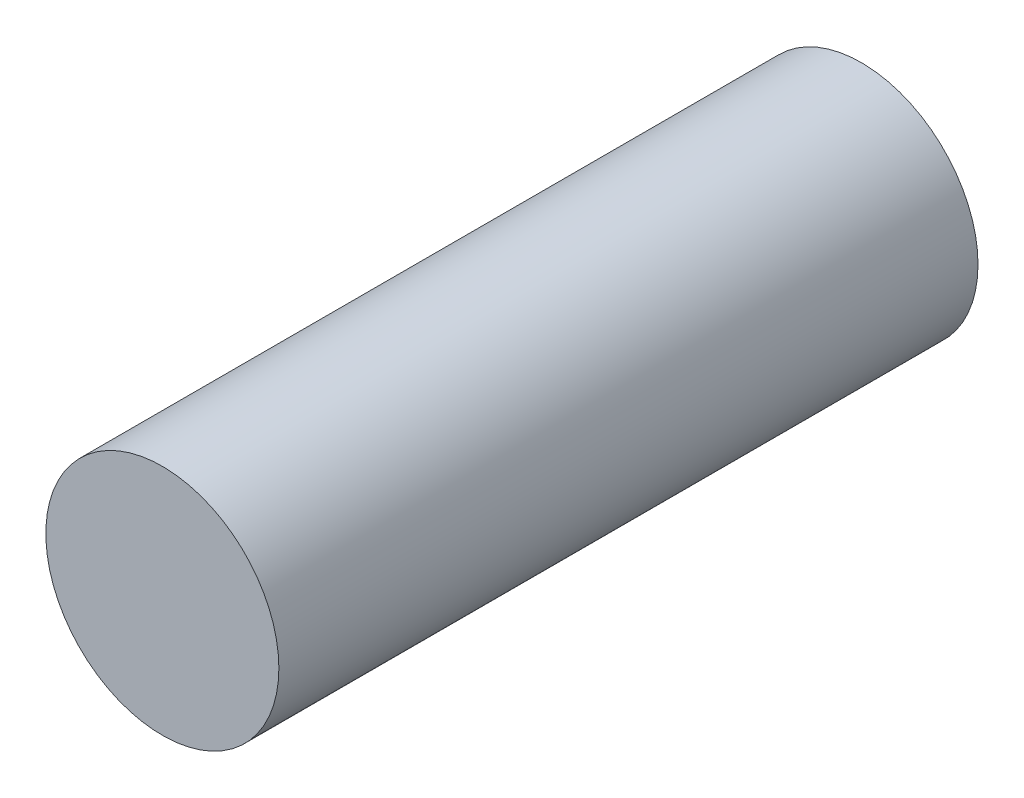
SolidWorks part; units mm, degrees
ref_plane "Alzado" through (0, 0, 0) normal (0, 0, 1) x (1, 0, 0)
ref_plane "Planta" through (0, 0, 0) normal (0, 1, 0) x (1, 0, 0)
ref_plane "Vista lateral" through (0, 0, 0) normal (1, 0, 0) x (0, 0, -1)
sketch "Croquis1" plane through (0, 0, 0) normal (0, 0, 1) x (1, 0, 0)
  circle A0 centre (0, 0) radius 0.5
  dimension "D1" = 1
extrude "Saliente-Extruir1" add sketch "Croquis1" along normal blind 3
